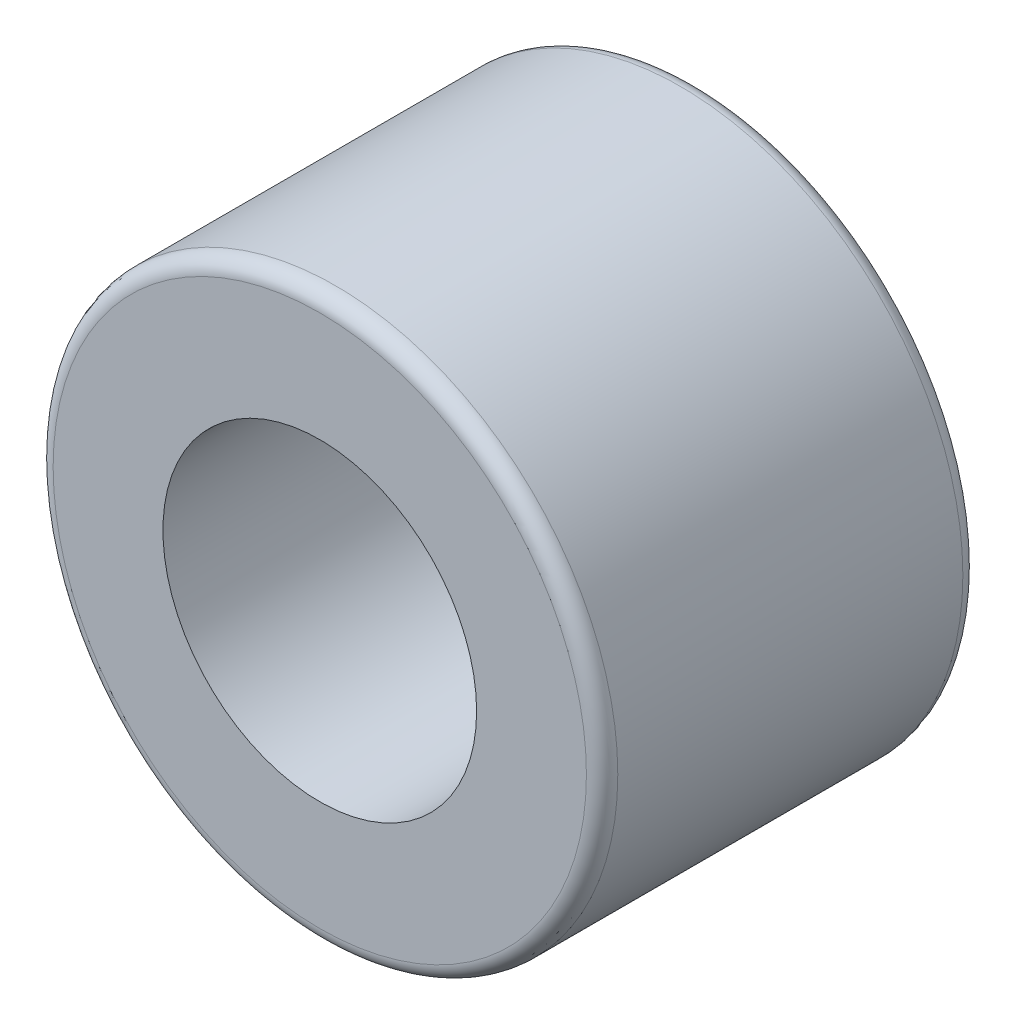
SolidWorks part; units mm, degrees
material "SS 304"
ref_plane "Front Plane" through (0, 0, 0) normal (0, 0, 1) x (1, 0, 0)
ref_plane "Top Plane" through (0, 0, 0) normal (0, 1, 0) x (1, 0, 0)
ref_plane "Right Plane" through (0, 0, 0) normal (1, 0, 0) x (0, 0, -1)
sketch "Sketch1" plane through (0, 0, 0) normal (0, 0, 1) x (1, 0, 0)
  circle A0 centre (0, 0) radius 14.2875
  circle A1 centre (0, 0) radius 7.9375
  dimension "D1" = 15.875
  dimension "Diameter" = 28.575
extrude "Extrude1" add sketch "Sketch1" along normal mid plane 19.05
fillet "Fillet1" radius 0.7937 2 edges at (14.2875, 0, -9.525) (14.2875, 0, 9.525)
